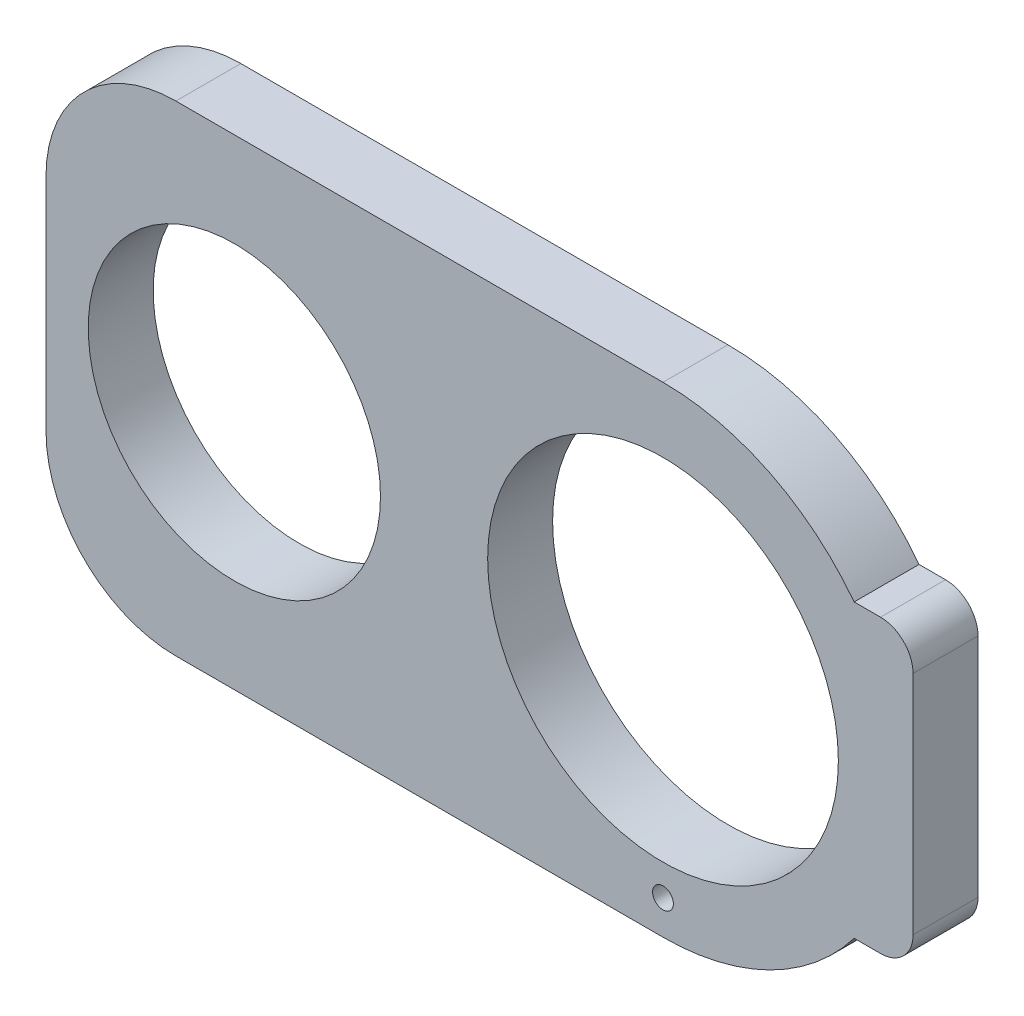
SolidWorks part; units mm, degrees
material "Сталь 08кп ГОСТ 535-88"
ref_plane "Спереди" through (0, 0, 0) normal (0, 0, 1) x (1, 0, 0)
ref_plane "Сверху" through (0, 0, 0) normal (0, 1, 0) x (1, 0, 0)
ref_plane "Справа" through (0, 0, 0) normal (1, 0, 0) x (0, 0, -1)
sketch "Sketch1" plane through (0, 0, 0) normal (0, 0, 1) x (1, 0, 0)
  line L0 (-86.593, -170.6459) -> (-114.093, -170.6459) construction
  line L8 (-48.093, -207.6459) -> (-123.093, -207.6459)
  line L10 (-48.093, -133.6459) -> (-123.093, -133.6459)
  line L11 (-143.093, -187.6459) -> (-143.093, -153.6459)
  line L13 (-18.6642, -193.0724) -> (-14.593, -193.0724)
  line L14 (-9.593, -188.0724) -> (-9.593, -153.2195)
  line L15 (-14.593, -148.2195) -> (-18.6642, -148.2195)
  line L17 (-48.093, -170.6459) -> (-143.093, -170.6459) construction
  arc A1 (-18.6642, -148.2195) -> (-48.093, -133.6459) centre (-48.093, -170.6459) ccw
  circle A2 centre (-48.093, -170.6459) radius 27
  circle A3 centre (-114.093, -170.6459) radius 22.5
  arc A6 (-123.093, -133.6459) -> (-143.093, -153.6459) centre (-123.093, -153.6459) ccw
  arc A7 (-123.093, -207.6459) -> (-143.093, -187.6459) centre (-123.093, -187.6459) cw
  arc A8 (-48.093, -207.6459) -> (-18.6642, -193.0724) centre (-48.093, -170.6459) ccw
  arc A15 (-14.593, -193.0724) -> (-9.593, -188.0724) centre (-14.593, -188.0724) ccw
  arc A16 (-9.593, -153.2195) -> (-14.593, -148.2195) centre (-14.593, -153.2195) ccw
  point P16 (-143.093, -133.6459)
  point P28 (-143.093, -133.6459)
  point P312 (-85.593, -170.6459)
  point P538 (-90.593, -165.1459)
  dimension "D1" = 27.5
  dimension "D2" = 45
  dimension "D6" = 74
  dimension "D3" = 20
extrude "Boss-Extrude1" add sketch "Sketch1" against normal blind 10
sketch "Sketch2" plane through (0, 0, 0) normal (0, 0, 1) x (1, 0, 0)
  circle A0 centre (-48.093, -202.3959) radius 1.6
  dimension "D1" = 3.2
extrude "Cut-Extrude1" cut sketch "Sketch2" against normal through all
